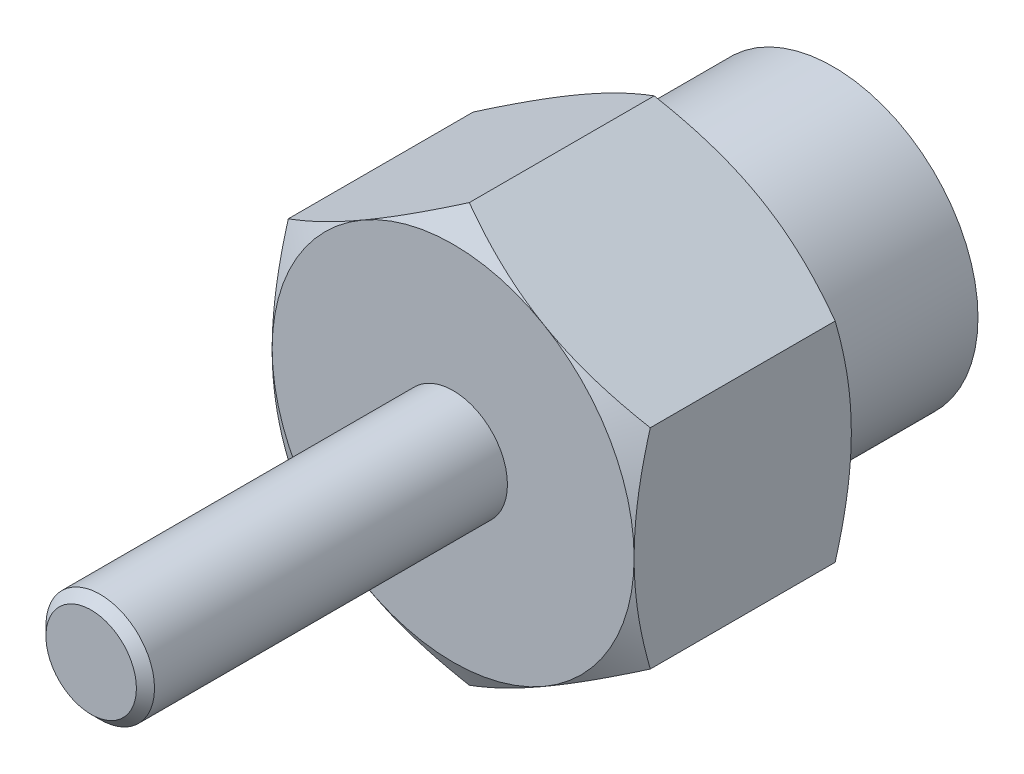
SolidWorks part; units mm, degrees
material "XC38"
ref_plane "Face" through (0, 0, 0) normal (0, 0, 1) x (1, 0, 0)
ref_plane "Dessus" through (0, 0, 0) normal (0, 1, 0) x (1, 0, 0)
ref_plane "Droite" through (0, 0, 0) normal (1, 0, 0) x (0, 0, -1)
sketch "Esquisse1" plane through (0, 0, 0) normal (0, 0, 1) x (1, 0, 0)
  line L1 (0, -5.7735) -> (5, -2.8868)
  line L2 (5, -2.8868) -> (5, 2.8868)
  line L3 (5, 2.8868) -> (0, 5.7735)
  line L4 (0, 5.7735) -> (-5, 2.8868)
  line L5 (-5, 2.8868) -> (-5, -2.8868)
  line L6 (-5, -2.8868) -> (0, -5.7735)
  circle A0 centre (0, 0) radius 5 construction
  dimension "D1" = 10
extrude "Boss.-Extru.1" add sketch "Esquisse1" along normal mid plane 6
sketch "Esquisse2" plane through (0, 0, 3) normal (0, 0, 1) x (1, 0, 0)
  circle A0 centre (0, 0) radius 5
extrude "Enlèv. mat.-Extru.1" cut sketch "Esquisse2" against normal blind 6 draft 60 flip side to cut
sketch "Esquisse3" plane through (0, 0, -3) normal (0, 0, -1) x (-1, 0, 0)
  circle A0 centre (0, 0) radius 4
  dimension "D1" = 8
extrude "Boss.-Extru.2" add sketch "Esquisse3" along normal blind 4.5
sketch "Esquisse4" plane through (0, 0, 3) normal (0, 0, 1) x (1, 0, 0)
  circle A0 centre (0, 0) radius 1.5
  dimension "D1" = 3
extrude "Boss.-Extru.3" add sketch "Esquisse4" along normal blind 10
cosmetic thread "Représentation de filetage1" parameters "D1"=4, "D2"=2.5
chamfer "Chanfrein1" distance 0.25 angle 45 1 edges at (1.5, 0, 13)
mirror "Symétrie1" about plane through (0, 0, 0) normal (0, 0, 1) of "Enlèv. mat.-Extru.1"
